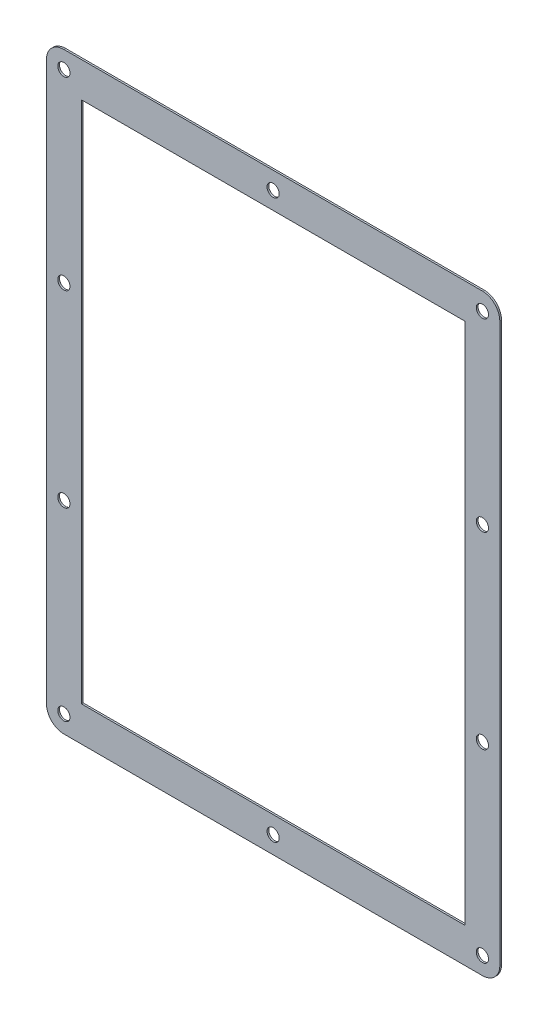
SolidWorks part; units mm, degrees
ref_plane "Front Plane" through (0, 0, 0) normal (0, 0, 1) x (1, 0, 0)
ref_plane "Top Plane" through (0, 0, 0) normal (0, 1, 0) x (1, 0, 0)
ref_plane "Right Plane" through (0, 0, 0) normal (1, 0, 0) x (0, 0, -1)
sketch "Sketch1" plane through (0, 0, 0) normal (0, 0, 1) x (1, 0, 0)
  line L10 (60, -85) -> (-60, -85)
  line L11 (65, -80) -> (65, 80)
  line L12 (60, 85) -> (-60, 85)
  line L13 (-65, -80) -> (-65, 80)
  line L14 (-55, -75) -> (-55, 75)
  line L15 (55, 75) -> (-55, 75)
  line L16 (55, -75) -> (55, 75)
  line L17 (55, -75) -> (-55, -75)
  line L18 (0, 0) -> (0, 112.7177) construction
  line L19 (0, 0) -> (126.367, 0) construction
  arc A10 (60, -85) -> (65, -80) centre (60, -80) ccw
  arc A11 (-60, -85) -> (-65, -80) centre (-60, -80) cw
  arc A12 (-60, 85) -> (-65, 80) centre (-60, 80) ccw
  arc A13 (65, 80) -> (60, 85) centre (60, 80) ccw
  arc A14 (-55, 75) -> (-55, 75) centre (-55, 75) ccw
  arc A15 (55, 75) -> (55, 75) centre (55, 75) ccw
  arc A16 (55, -75) -> (55, -75) centre (55, -75) ccw
  arc A17 (-55, -75) -> (-55, -75) centre (-55, -75) cw
  circle A18 centre (60, -27) radius 1.75
  circle A19 centre (60, -80) radius 1.75
  circle A20 centre (-60, -27) radius 1.75
  circle A21 centre (-60, -80) radius 1.75
  circle A22 centre (0, -80) radius 1.75
  circle A23 centre (60, 27) radius 1.75
  circle A24 centre (60, 80) radius 1.75
  circle A25 centre (0, 80) radius 1.75
  circle A26 centre (-60, 27) radius 1.75
  circle A27 centre (-60, 80) radius 1.75
  dimension "D3" = 5
  dimension "D4" = 3.5
  dimension "D5" = 3.5
  dimension "D6" = 3.5
  dimension "D1" = 10
  dimension "D2" = 27
  dimension "D7" = 60
  dimension "D8" = 80
  dimension "D9" = 80
  dimension "D10" = 60
  dimension "D11" = 60
  dimension "D12" = 53
  dimension "D13" = 54
  dimension "D14" = 53
  dimension "D15" = 60
  dimension "D16" = 60
  dimension "D17" = 53
  dimension "D18" = 54
  dimension "D19" = 53
extrude "Boss-Extrude1" add sketch "Sketch1" along normal blind 0.5
equation "\"0.5.000000mm\"=10"
